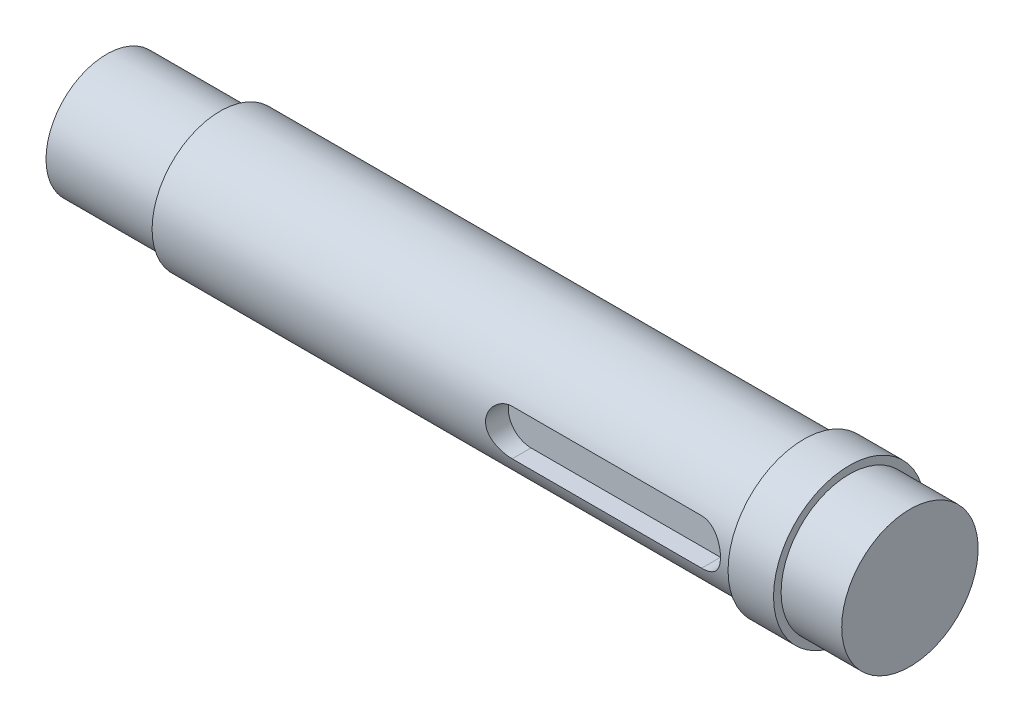
SolidWorks part; units mm, degrees
material "普通碳钢"
ref_plane "前视基准面" through (0, 0, 0) normal (0, 0, 1) x (1, 0, 0)
ref_plane "上视基准面" through (0, 0, 0) normal (0, 1, 0) x (1, 0, 0)
ref_plane "右视基准面" through (0, 0, 0) normal (1, 0, 0) x (0, 0, -1)
sketch "草图2" plane through (0, 0, 0) normal (0, 1, 0) x (1, 0, 0)
  line L0 (0, 0) -> (165.8153, 0) construction
  line L1 (0, 0) -> (0, 8)
  line L2 (15, 9) -> (92, 9)
  line L3 (92, 9) -> (92, 10)
  line L4 (92, 10) -> (98, 10)
  line L5 (15, 9) -> (15, 8)
  line L6 (15, 8) -> (0, 8)
  line L7 (98, 10) -> (98, 9)
  line L8 (98, 9) -> (106, 9)
  line L11 (106, 9) -> (106, 0)
  line L12 (0, 0) -> (106, 0)
  dimension "D1" = 106
  dimension "D2" = 8
  dimension "D3" = 15
  dimension "D4" = 77
  dimension "D5" = 9
  dimension "D6" = 10
  dimension "D7" = 9
  dimension "D8" = 8
  dimension "D9" = 6
revolve "旋转1" add sketch "草图2" angle 360 about L0
cosmetic thread "装饰螺纹线1" parameters "D1"=13, "D2"=13.835
ref_plane "基准面1" through (0, 0, 9) normal (0, 0, 1) x (1, 0, 0)
sketch "草图4" plane through (0, 0, 9) normal (0, 0, 1) x (1, 0, 0)
  line L0 (0, 0) -> (48.9051, 0) construction
  line L1 (62, 0) -> (87, 0) construction
  line L2 (62, 3) -> (87, 3)
  line L3 (62, -3) -> (87, -3)
  line L4 (92, 9) -> (92, -9) construction
  arc A0 (62, 3) -> (62, -3) centre (62, 0) ccw
  arc A1 (87, -3) -> (87, 3) centre (87, 0) ccw
  point P5 (74.5, 0)
  dimension "D1" = 3
  dimension "D2" = 25
  dimension "D3" = 5
extrude "切除-拉伸2" cut sketch "草图4" against normal blind 3
equation "\"16。5\"=23.2"
